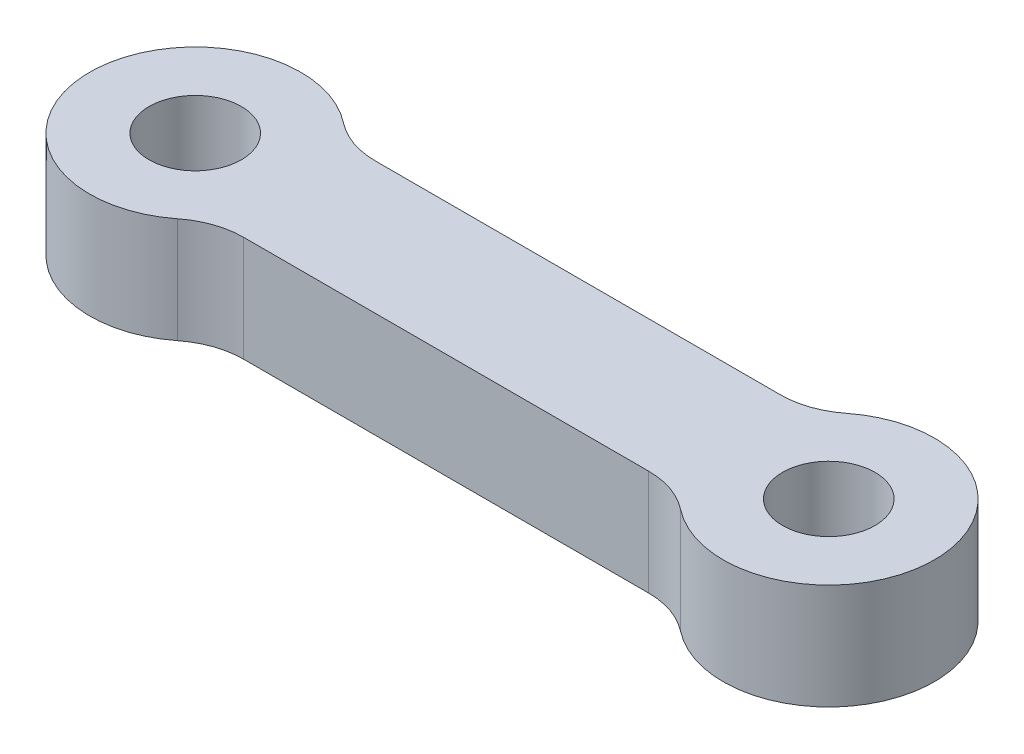
SolidWorks part; units mm, degrees
ref_plane "Front Plane" through (0, 0, 0) normal (0, 0, 1) x (1, 0, 0)
ref_plane "Top Plane" through (0, 0, 0) normal (0, 1, 0) x (1, 0, 0)
ref_plane "Right Plane" through (0, 0, 0) normal (1, 0, 0) x (0, 0, -1)
sketch "Sketch1" plane through (0, 0, 0) normal (0, 1, 0) x (1, 0, 0)
  line L0 (0, 0) -> (24, 0) construction
  line L1 (3.1225, 2.5) -> (20.8775, 2.5)
  line L2 (3.1225, -2.5) -> (20.8775, -2.5)
  circle A0 centre (0, 0) radius 4
  circle A1 centre (24, 0) radius 4
  circle A2 centre (0, 0) radius 1.75
  circle A3 centre (24, 0) radius 1.75
  dimension "D1" = 8
  dimension "D3" = 8
  dimension "D5" = 3.5
  dimension "D6" = 3.5
  dimension "D2" = 24
  dimension "D4" = 2.5
extrude "Boss-Extrude1" add sketch "Sketch1" along normal blind 4
fillet "Fillet1" radius 3 4 edges at (3.1225, 2, 2.5) (20.8775, 2, 2.5) (20.8775, 2, -2.5) (3.1225, 2, -2.5)
